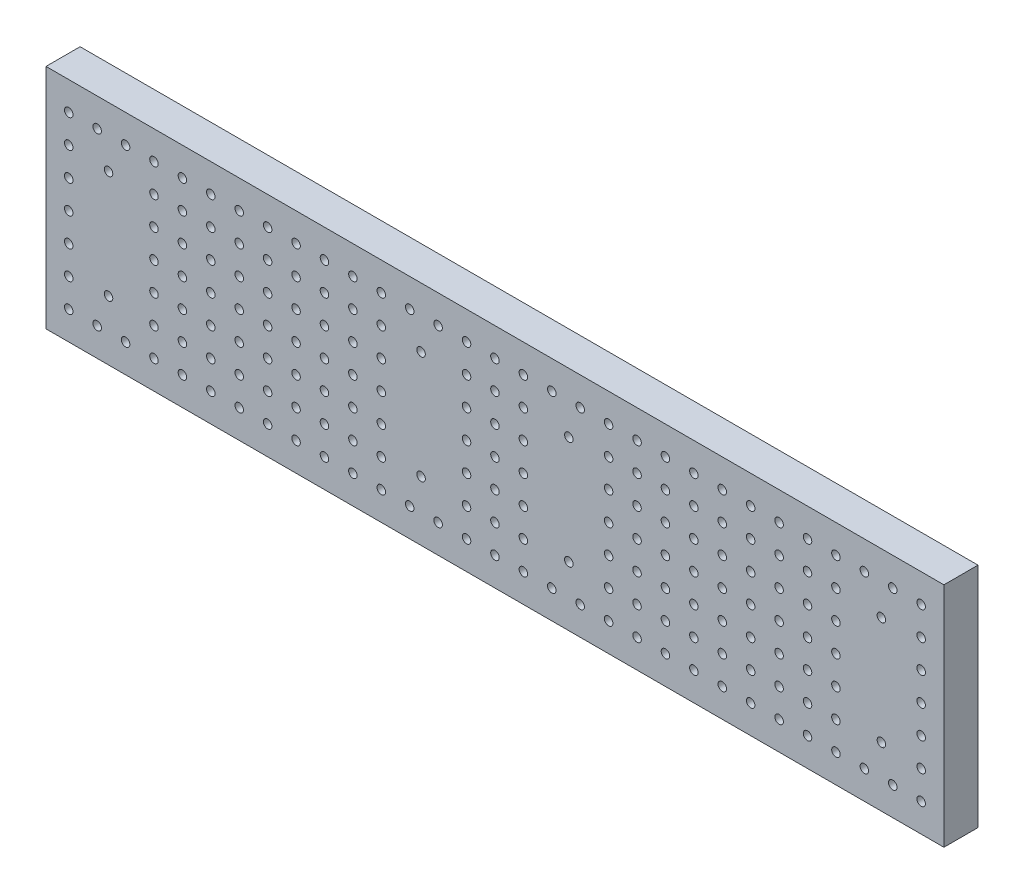
SolidWorks part; units mm, degrees
ref_plane "Спереди" through (0, 0, 0) normal (0, 0, 1) x (1, 0, 0)
ref_plane "Сверху" through (0, 0, 0) normal (0, 1, 0) x (1, 0, 0)
ref_plane "Справа" through (0, 0, 0) normal (1, 0, 0) x (0, 0, -1)
other "Configuration Table"
sketch "Эскиз1" plane through (0, 0, 0) normal (0, 0, 1) x (1, 0, 0)
  line L0 (79, 40) -> (79, 0) construction
  line L1 (0, 0) -> (158, 0)
  line L2 (0, 0) -> (0, 40)
  line L3 (0, 40) -> (158, 40)
  line L4 (158, 0) -> (158, 40)
  line L5 (38.5, 40) -> (38.5, 0) construction
  line L6 (0, 20) -> (158, 20) construction
  circle A0 centre (11, 29.5) radius 0.75
  circle A1 centre (66, 29.5) radius 0.75
  circle A2 centre (66, 10.5) radius 0.75
  circle A3 centre (11, 10.5) radius 0.75
  circle A4 centre (92, 10.5) radius 0.75
  circle A5 centre (92, 29.5) radius 0.75
  circle A6 centre (147, 10.5) radius 0.75
  circle A7 centre (147, 29.5) radius 0.75
  dimension "D4" = 1.5
  dimension "D1" = 55
  dimension "D2" = 19
  dimension "D3" = 40
  dimension "D5" = 26
  dimension "D6" = 11
extrude "Бобышка-Вытянуть1" add sketch "Эскиз1" along normal blind 6
sketch "Эскиз2" plane through (0, 0, 6) normal (0, 0, 1) x (1, 0, 0)
  line L0 (158, 40) -> (0, 40) construction
  line L1 (0, 40) -> (0, 0) construction
  circle A0 centre (4, 35) radius 0.75
  circle A1 centre (9, 35) radius 0.75
  circle A2 centre (14, 35) radius 0.75
  circle A3 centre (19, 35) radius 0.75
  circle A4 centre (24, 35) radius 0.75
  circle A5 centre (29, 35) radius 0.75
  circle A6 centre (34, 35) radius 0.75
  circle A7 centre (39, 35) radius 0.75
  circle A8 centre (44, 35) radius 0.75
  circle A9 centre (49, 35) radius 0.75
  circle A10 centre (54, 35) radius 0.75
  circle A11 centre (59, 35) radius 0.75
  circle A12 centre (64, 35) radius 0.75
  circle A13 centre (69, 35) radius 0.75
  circle A14 centre (74, 35) radius 0.75
  circle A15 centre (79, 35) radius 0.75
  circle A16 centre (84, 35) radius 0.75
  circle A17 centre (89, 35) radius 0.75
  circle A18 centre (94, 35) radius 0.75
  circle A19 centre (99, 35) radius 0.75
  circle A20 centre (104, 35) radius 0.75
  circle A21 centre (109, 35) radius 0.75
  circle A22 centre (114, 35) radius 0.75
  circle A23 centre (119, 35) radius 0.75
  circle A24 centre (124, 35) radius 0.75
  circle A25 centre (129, 35) radius 0.75
  circle A26 centre (134, 35) radius 0.75
  circle A27 centre (139, 35) radius 0.75
  circle A28 centre (144, 35) radius 0.75
  circle A29 centre (149, 35) radius 0.75
  circle A30 centre (154, 35) radius 0.75
  circle A33 centre (19, 30) radius 0.75
  circle A34 centre (24, 30) radius 0.75
  circle A35 centre (29, 30) radius 0.75
  circle A36 centre (34, 30) radius 0.75
  circle A37 centre (39, 30) radius 0.75
  circle A38 centre (44, 30) radius 0.75
  circle A39 centre (49, 30) radius 0.75
  circle A40 centre (54, 30) radius 0.75
  circle A41 centre (59, 30) radius 0.75
  circle A44 centre (74, 30) radius 0.75
  circle A45 centre (79, 30) radius 0.75
  circle A46 centre (84, 30) radius 0.75
  circle A49 centre (99, 30) radius 0.75
  circle A50 centre (104, 30) radius 0.75
  circle A51 centre (109, 30) radius 0.75
  circle A52 centre (114, 30) radius 0.75
  circle A53 centre (119, 30) radius 0.75
  circle A54 centre (124, 30) radius 0.75
  circle A55 centre (129, 30) radius 0.75
  circle A56 centre (134, 30) radius 0.75
  circle A57 centre (139, 30) radius 0.75
  circle A60 centre (154, 30) radius 0.75
  circle A63 centre (19, 25) radius 0.75
  circle A64 centre (24, 25) radius 0.75
  circle A65 centre (29, 25) radius 0.75
  circle A66 centre (34, 25) radius 0.75
  circle A67 centre (39, 25) radius 0.75
  circle A68 centre (44, 25) radius 0.75
  circle A69 centre (49, 25) radius 0.75
  circle A70 centre (54, 25) radius 0.75
  circle A71 centre (59, 25) radius 0.75
  circle A74 centre (74, 25) radius 0.75
  circle A75 centre (79, 25) radius 0.75
  circle A76 centre (84, 25) radius 0.75
  circle A79 centre (99, 25) radius 0.75
  circle A80 centre (104, 25) radius 0.75
  circle A81 centre (109, 25) radius 0.75
  circle A82 centre (114, 25) radius 0.75
  circle A83 centre (119, 25) radius 0.75
  circle A84 centre (124, 25) radius 0.75
  circle A85 centre (129, 25) radius 0.75
  circle A86 centre (134, 25) radius 0.75
  circle A87 centre (139, 25) radius 0.75
  circle A90 centre (154, 25) radius 0.75
  circle A93 centre (19, 20) radius 0.75
  circle A94 centre (24, 20) radius 0.75
  circle A95 centre (29, 20) radius 0.75
  circle A96 centre (34, 20) radius 0.75
  circle A97 centre (39, 20) radius 0.75
  circle A98 centre (44, 20) radius 0.75
  circle A99 centre (49, 20) radius 0.75
  circle A100 centre (54, 20) radius 0.75
  circle A101 centre (59, 20) radius 0.75
  circle A104 centre (74, 20) radius 0.75
  circle A105 centre (79, 20) radius 0.75
  circle A106 centre (84, 20) radius 0.75
  circle A109 centre (99, 20) radius 0.75
  circle A110 centre (104, 20) radius 0.75
  circle A111 centre (109, 20) radius 0.75
  circle A112 centre (114, 20) radius 0.75
  circle A113 centre (119, 20) radius 0.75
  circle A114 centre (124, 20) radius 0.75
  circle A115 centre (129, 20) radius 0.75
  circle A116 centre (134, 20) radius 0.75
  circle A117 centre (139, 20) radius 0.75
  circle A120 centre (154, 20) radius 0.75
  circle A123 centre (19, 15) radius 0.75
  circle A124 centre (24, 15) radius 0.75
  circle A125 centre (29, 15) radius 0.75
  circle A126 centre (34, 15) radius 0.75
  circle A127 centre (39, 15) radius 0.75
  circle A128 centre (44, 15) radius 0.75
  circle A129 centre (49, 15) radius 0.75
  circle A130 centre (54, 15) radius 0.75
  circle A131 centre (59, 15) radius 0.75
  circle A134 centre (74, 15) radius 0.75
  circle A135 centre (79, 15) radius 0.75
  circle A136 centre (84, 15) radius 0.75
  circle A139 centre (99, 15) radius 0.75
  circle A140 centre (104, 15) radius 0.75
  circle A141 centre (109, 15) radius 0.75
  circle A142 centre (114, 15) radius 0.75
  circle A143 centre (119, 15) radius 0.75
  circle A144 centre (124, 15) radius 0.75
  circle A145 centre (129, 15) radius 0.75
  circle A146 centre (134, 15) radius 0.75
  circle A147 centre (139, 15) radius 0.75
  circle A150 centre (154, 15) radius 0.75
  circle A153 centre (19, 10) radius 0.75
  circle A154 centre (24, 10) radius 0.75
  circle A155 centre (29, 10) radius 0.75
  circle A156 centre (34, 10) radius 0.75
  circle A157 centre (39, 10) radius 0.75
  circle A158 centre (44, 10) radius 0.75
  circle A159 centre (49, 10) radius 0.75
  circle A160 centre (54, 10) radius 0.75
  circle A161 centre (59, 10) radius 0.75
  circle A164 centre (74, 10) radius 0.75
  circle A165 centre (79, 10) radius 0.75
  circle A166 centre (84, 10) radius 0.75
  circle A169 centre (99, 10) radius 0.75
  circle A170 centre (104, 10) radius 0.75
  circle A171 centre (109, 10) radius 0.75
  circle A172 centre (114, 10) radius 0.75
  circle A173 centre (119, 10) radius 0.75
  circle A174 centre (124, 10) radius 0.75
  circle A175 centre (129, 10) radius 0.75
  circle A176 centre (134, 10) radius 0.75
  circle A177 centre (139, 10) radius 0.75
  circle A180 centre (154, 10) radius 0.75
  circle A181 centre (9, 5) radius 0.75
  circle A182 centre (14, 5) radius 0.75
  circle A183 centre (19, 5) radius 0.75
  circle A184 centre (24, 5) radius 0.75
  circle A185 centre (29, 5) radius 0.75
  circle A186 centre (34, 5) radius 0.75
  circle A187 centre (39, 5) radius 0.75
  circle A188 centre (44, 5) radius 0.75
  circle A189 centre (49, 5) radius 0.75
  circle A190 centre (54, 5) radius 0.75
  circle A191 centre (59, 5) radius 0.75
  circle A192 centre (64, 5) radius 0.75
  circle A193 centre (69, 5) radius 0.75
  circle A194 centre (74, 5) radius 0.75
  circle A195 centre (79, 5) radius 0.75
  circle A196 centre (84, 5) radius 0.75
  circle A197 centre (89, 5) radius 0.75
  circle A198 centre (94, 5) radius 0.75
  circle A199 centre (99, 5) radius 0.75
  circle A200 centre (104, 5) radius 0.75
  circle A201 centre (109, 5) radius 0.75
  circle A202 centre (114, 5) radius 0.75
  circle A203 centre (119, 5) radius 0.75
  circle A204 centre (124, 5) radius 0.75
  circle A205 centre (129, 5) radius 0.75
  circle A206 centre (134, 5) radius 0.75
  circle A207 centre (139, 5) radius 0.75
  circle A208 centre (144, 5) radius 0.75
  circle A209 centre (149, 5) radius 0.75
  circle A210 centre (154, 5) radius 0.75
  circle A211 centre (4, 30) radius 0.75
  circle A212 centre (4, 25) radius 0.75
  circle A213 centre (4, 20) radius 0.75
  circle A214 centre (4, 15) radius 0.75
  circle A215 centre (4, 10) radius 0.75
  circle A216 centre (4, 5) radius 0.75
  circle A217 centre (9, 30) radius 0.75 [skipped]
  circle A218 centre (14, 30) radius 0.75 [skipped]
  circle A219 centre (9, 25) radius 0.75 [skipped]
  circle A220 centre (14, 25) radius 0.75 [skipped]
  circle A221 centre (9, 20) radius 0.75 [skipped]
  circle A222 centre (14, 20) radius 0.75 [skipped]
  circle A223 centre (9, 15) radius 0.75 [skipped]
  circle A224 centre (14, 15) radius 0.75 [skipped]
  circle A225 centre (9, 10) radius 0.75 [skipped]
  circle A226 centre (14, 10) radius 0.75 [skipped]
  circle A227 centre (64, 30) radius 0.75 [skipped]
  circle A228 centre (69, 30) radius 0.75 [skipped]
  circle A229 centre (64, 25) radius 0.75 [skipped]
  circle A230 centre (69, 25) radius 0.75 [skipped]
  circle A231 centre (64, 20) radius 0.75 [skipped]
  circle A232 centre (69, 20) radius 0.75 [skipped]
  circle A233 centre (64, 15) radius 0.75 [skipped]
  circle A234 centre (69, 15) radius 0.75 [skipped]
  circle A235 centre (64, 10) radius 0.75 [skipped]
  circle A236 centre (69, 10) radius 0.75 [skipped]
  circle A237 centre (89, 30) radius 0.75 [skipped]
  circle A238 centre (94, 30) radius 0.75 [skipped]
  circle A239 centre (89, 25) radius 0.75 [skipped]
  circle A240 centre (94, 25) radius 0.75 [skipped]
  circle A241 centre (89, 20) radius 0.75 [skipped]
  circle A242 centre (94, 20) radius 0.75 [skipped]
  circle A243 centre (89, 15) radius 0.75 [skipped]
  circle A244 centre (94, 15) radius 0.75 [skipped]
  circle A245 centre (89, 10) radius 0.75 [skipped]
  circle A246 centre (94, 10) radius 0.75 [skipped]
  circle A247 centre (144, 30) radius 0.75 [skipped]
  circle A248 centre (149, 30) radius 0.75 [skipped]
  circle A249 centre (144, 25) radius 0.75 [skipped]
  circle A250 centre (149, 25) radius 0.75 [skipped]
  circle A251 centre (144, 20) radius 0.75 [skipped]
  circle A252 centre (149, 20) radius 0.75 [skipped]
  circle A253 centre (144, 15) radius 0.75 [skipped]
  circle A254 centre (149, 15) radius 0.75 [skipped]
  circle A255 centre (144, 10) radius 0.75 [skipped]
  circle A256 centre (149, 10) radius 0.75 [skipped]
  point P6 (0, 0)
  point P7 (0, 0)
  dimension "D1" = 1.5
  dimension "D2" = 5
  dimension "D3" = 4
  dimension "D4" = 31
  dimension "D5" = 7
extrude "Вырез-Вытянуть1" cut sketch "Эскиз2" against normal blind 6
